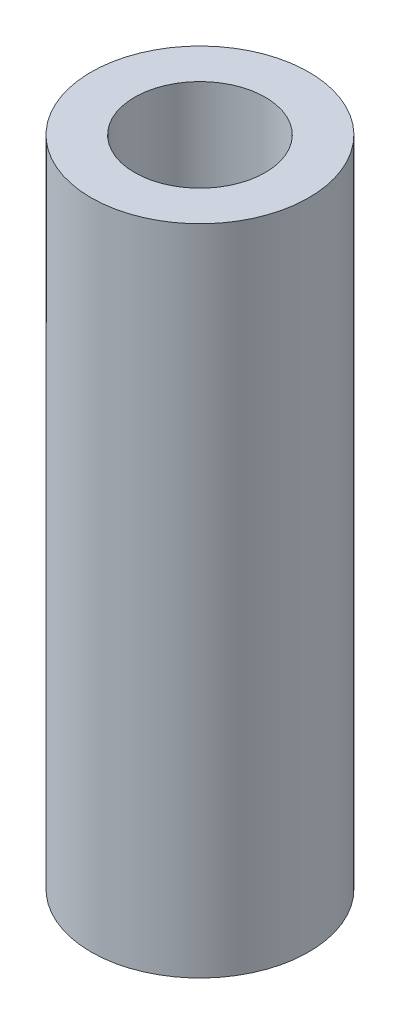
SolidWorks part; units mm, degrees
ref_plane "Front Plane" through (0, 0, 0) normal (0, 0, 1) x (1, 0, 0)
ref_plane "Top Plane" through (0, 0, 0) normal (0, 1, 0) x (1, 0, 0)
ref_plane "Right Plane" through (0, 0, 0) normal (1, 0, 0) x (0, 0, -1)
sketch "Sketch1" plane through (0, 0, 0) normal (0, 1, 0) x (1, 0, 0)
  circle A0 centre (0, 0) radius 1.5
  circle A1 centre (0, 0) radius 2.5
  dimension "D1" = 3
  dimension "D2" = 5
extrude "Boss-Extrude1" add sketch "Sketch1" along normal blind 15
